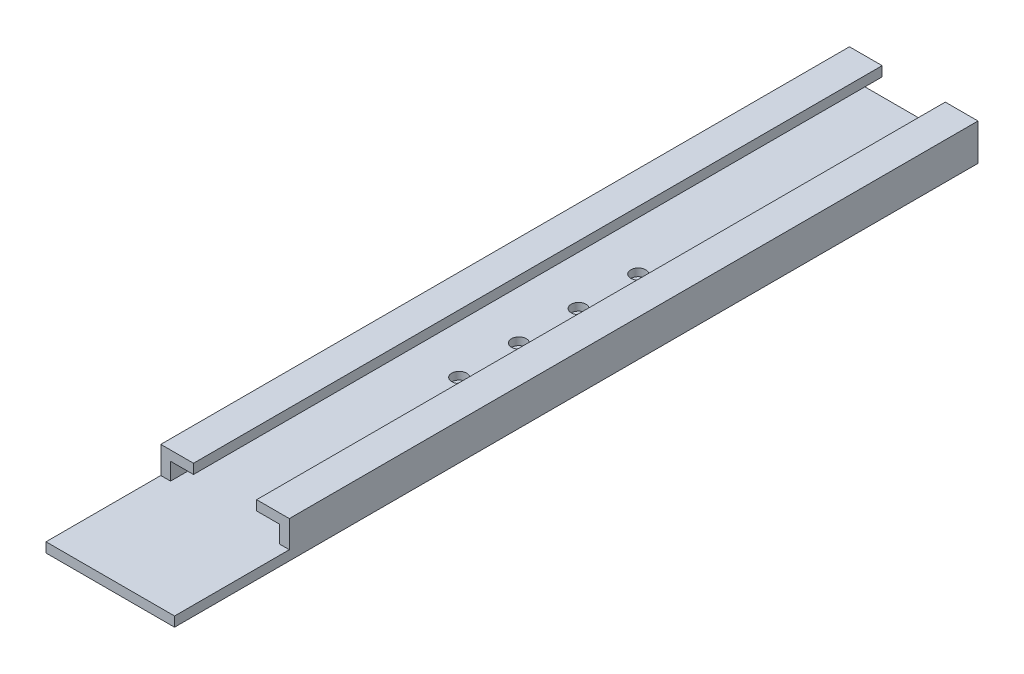
SolidWorks part; units mm, degrees
material "3003 Alloy"
ref_plane "Front Plane" through (0, 0, 0) normal (0, 0, 1) x (1, 0, 0)
ref_plane "Top Plane" through (0, 0, 0) normal (0, 1, 0) x (1, 0, 0)
ref_plane "Right Plane" through (0, 0, 0) normal (1, 0, 0) x (0, 0, -1)
sketch "Sketch1" plane through (0, 0, 0) normal (0, 0, 1) x (1, 0, 0)
  line L0 (0, 0) -> (95, 0)
  line L1 (95, 0) -> (95, 15)
  line L2 (95, 15) -> (75, 15)
  line L3 (0, 0) -> (0, 15)
  line L4 (0, 15) -> (20, 15)
  line L5 (-8.5, 23.5) -> (20, 23.5)
  line L6 (-8.5, -8.5) -> (-8.5, 23.5)
  line L7 (-8.5, -8.5) -> (103.5, -8.5)
  line L8 (103.5, -8.5) -> (103.5, 23.5)
  line L9 (103.5, 23.5) -> (75, 23.5)
  line L10 (20, 15) -> (20, 23.5)
  line L11 (75, 15) -> (75, 23.5)
  dimension "D1" = 95
  dimension "D2" = 15
  dimension "D3" = 20
  dimension "D4" = 8.5
extrude "Boss-Extrude1" add sketch "Sketch1" along normal blind 600
sketch "Sketch4" plane through (0, -8.5, 0) normal (0, -1, 0) x (1, 0, 0)
  line L0 (103.5, 600) -> (103.5, 0) construction
  line L1 (-8.5, 600) -> (103.5, 600)
  line L2 (-8.5, 600) -> (-8.5, 700)
  line L3 (-8.5, 700) -> (103.5, 700)
  line L4 (103.5, 600) -> (103.5, 700)
  dimension "D1" = 100
extrude "Boss-Extrude2" add sketch "Sketch4" against normal blind 8.5
sketch "Sketch6" plane through (0, 0, 0) normal (0, 1, 0) x (1, 0, 0)
  line L0 (95, 0) -> (0, 0) construction
  circle A0 centre (47.5, -240) radius 3.3
  circle A1 centre (47.5, -292) radius 3.3
  circle A2 centre (47.5, -344) radius 3.3
  circle A3 centre (47.5, -396) radius 3.3
  point P10 (47.5, 0)
  dimension "D1" = 6.6
  dimension "D3" = 52
  dimension "D4" = 52
  dimension "D5" = 240
  dimension "D2" = 52
extrude "Cut-Extrude1" cut sketch "Sketch6" against normal through all
sketch "Sketch7" plane through (0, 0, 0) normal (0, 1, 0) x (1, 0, 0)
  circle A0 centre (47.5, -240) radius 6.5
  circle A1 centre (47.5, -292) radius 6.5
  circle A2 centre (47.5, -344) radius 6.5
  circle A3 centre (47.5, -396) radius 6.5
  dimension "D1" = 13
extrude "Cut-Extrude2" cut sketch "Sketch7" against normal blind 6.6
